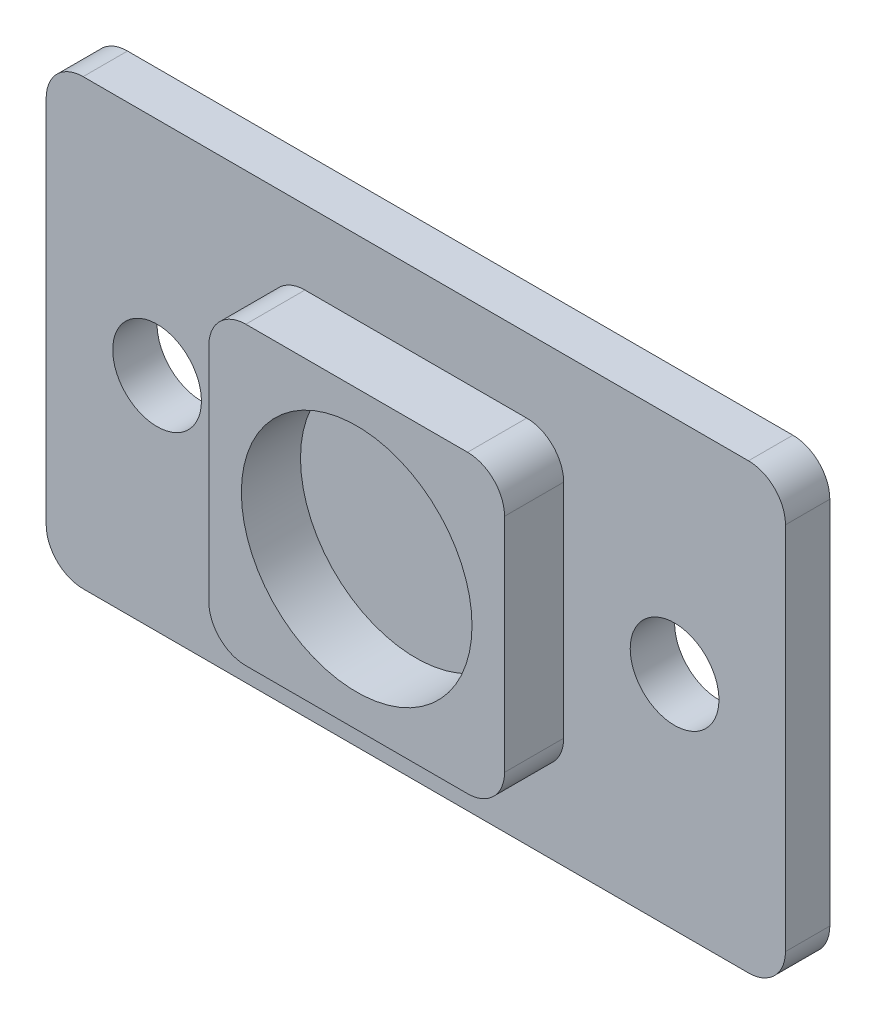
SolidWorks part; units mm, degrees
ref_plane "Ebene vorne" through (0, 0, 0) normal (0, 0, 1) x (1, 0, 0)
ref_plane "Ebene oben" through (0, 0, 0) normal (0, 1, 0) x (1, 0, 0)
ref_plane "Ebene rechts" through (0, 0, 0) normal (1, 0, 0) x (0, 0, -1)
sketch "Sketch1" plane through (0, 0, 0) normal (0, 0, 1) x (1, 0, 0)
  line L0 (-25, 15) -> (25, 15)
  line L1 (25, 15) -> (25, -15)
  line L2 (25, -15) -> (-25, -15)
  line L3 (-25, -15) -> (-25, 15)
  line L4 (0, 15) -> (0, -15) construction
  circle A1 centre (-17.5, 0) radius 3
  circle A3 centre (17.5, 0) radius 3
  dimension "D1" = 25
  dimension "D5" = 17.5
  dimension "D6" = 6
  dimension "D2" = 50
  dimension "D3" = 15
  dimension "D4" = 30
  dimension "D7" = 15
extrude "Boss-Extrude1" add sketch "Sketch1" along normal mid plane 3
fillet "Fillet1" radius 2.5 4 edges at (-25, -15, 0) (25, -15, 0) (25, 15, 0) (-25, 15, 0)
sketch "Sketch2" plane through (0, 0, 1.5) normal (0, 0, 1) x (1, 0, 0)
  line L1 (7.5, -10) -> (-7.5, -10)
  line L2 (10, -7.5) -> (10, 7.5)
  line L3 (7.5, 10) -> (-7.5, 10)
  line L4 (-10, -7.5) -> (-10, 7.5)
  line L5 (10, -10) -> (-10, 10) construction
  line L6 (10, 10) -> (-10, -10) construction
  circle A0 centre (0, 0) radius 7.8
  arc A1 (-7.5, -10) -> (-10, -7.5) centre (-7.5, -7.5) cw
  arc A2 (7.5, -10) -> (10, -7.5) centre (7.5, -7.5) ccw
  arc A3 (10, 7.5) -> (7.5, 10) centre (7.5, 7.5) ccw
  arc A4 (-7.5, 10) -> (-10, 7.5) centre (-7.5, 7.5) ccw
  point P0 (0, 0)
  dimension "D3" = 15.6
  dimension "D4" = 2.5
  dimension "D1" = 20
  dimension "D2" = 20
extrude "Boss-Extrude2" add sketch "Sketch2" along normal blind 4
